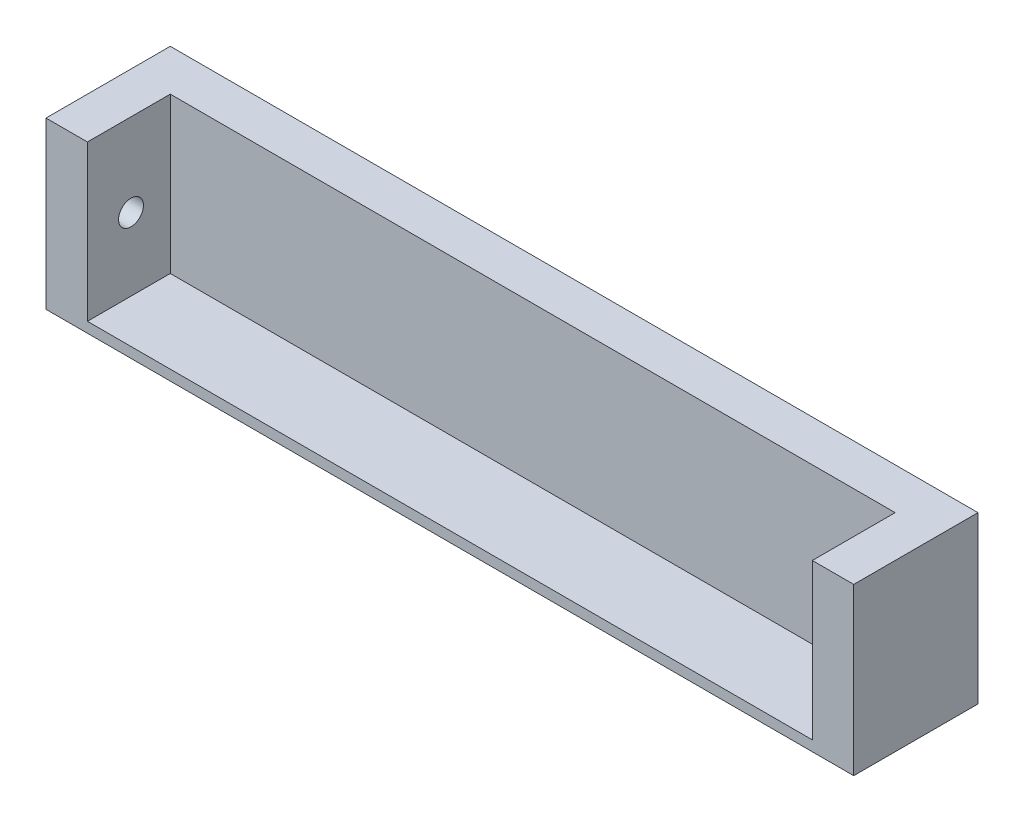
SolidWorks part; units mm, degrees
material "Beech"
ref_plane "Front Plane" through (0, 0, 0) normal (0, 0, 1) x (1, 0, 0)
ref_plane "Top Plane" through (0, 0, 0) normal (0, 1, 0) x (1, 0, 0)
ref_plane "Right Plane" through (0, 0, 0) normal (1, 0, 0) x (0, 0, -1)
sketch "Sketch2" plane through (0, 0, 0) normal (0, 0, 1) x (1, 0, 0)
  line L1 (0, 0) -> (390, 0)
  line L2 (0, 0) -> (0, 80)
  line L3 (0, 80) -> (390, 80)
  line L4 (390, 0) -> (390, 80)
  dimension "D1" = 390
  dimension "D2" = 80
extrude "Boss-Extrude1" add sketch "Sketch2" along normal blind 60
sketch "Sketch4" plane through (0, 0, 60) normal (0, 0, 1) x (1, 0, 0)
  line L0 (390, 80) -> (0, 80) construction
  line L1 (20, 80) -> (370, 80)
  line L2 (20, 80) -> (20, 5)
  line L3 (20, 5) -> (370, 5)
  line L4 (370, 80) -> (370, 5)
  dimension "D1" = 20
  dimension "D2" = 20
  dimension "D3" = 5
extrude "Cut-Extrude1" cut sketch "Sketch4" against normal blind 40
sketch "Sketch5" plane through (20, 0, 0) normal (1, 0, 0) x (0, 0, -1)
  circle A0 centre (-38.9577, 40) radius 6
  dimension "D3" = 12
  dimension "D1" = 21.0423
  dimension "D2" = 35
extrude "Cut-Extrude2" cut sketch "Sketch5" against normal blind 10 and the other way blind 360
